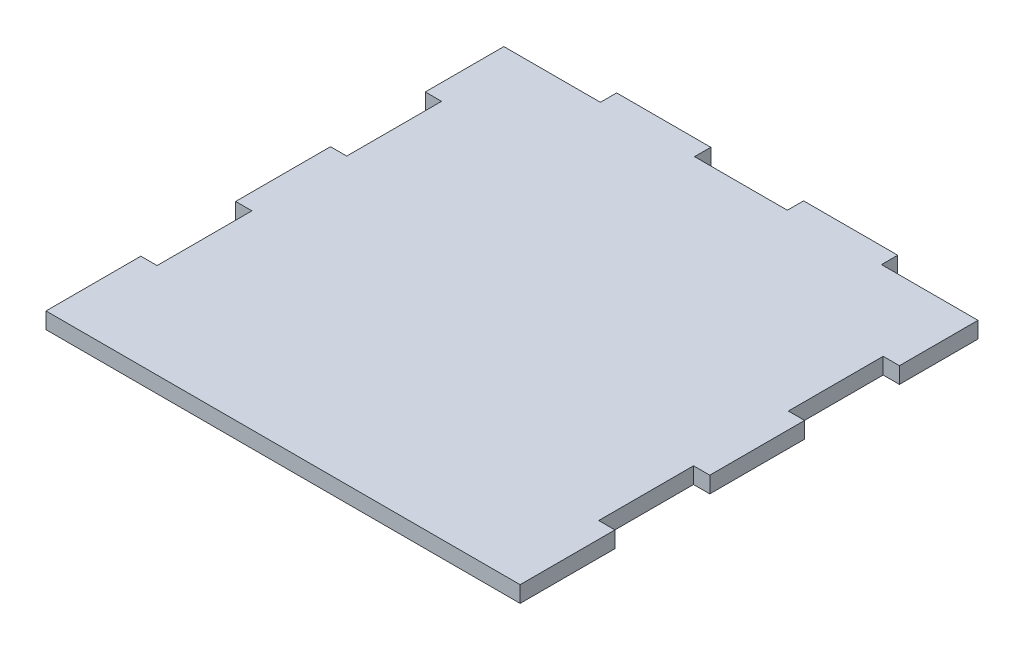
SolidWorks part; units mm, degrees
material "Maple"
ref_plane "Front Plane" through (0, 0, 0) normal (0, 0, 1) x (1, 0, 0)
ref_plane "Top Plane" through (0, 0, 0) normal (0, 1, 0) x (1, 0, 0)
ref_plane "Right Plane" through (0, 0, 0) normal (1, 0, 0) x (0, 0, -1)
sketch "Sketch1" plane through (0, 0, 0) normal (0, 1, 0) x (1, 0, 0)
  line L0 (209.25, 350) -> (278.75, 350)
  line L1 (0, 0) -> (350, 0)
  line L2 (0, 0) -> (0, 70)
  line L3 (71.25, 350) -> (140.75, 350)
  line L4 (350, 0) -> (350, 70)
  line L7 (0, 338) -> (71.25, 338)
  line L8 (71.25, 350) -> (71.25, 338)
  line L11 (350, 338) -> (278.75, 338)
  line L12 (278.75, 350) -> (278.75, 338)
  line L14 (140.75, 350) -> (140.75, 338)
  line L15 (140.75, 338) -> (209.25, 338)
  line L16 (209.25, 350) -> (209.25, 338)
  line L17 (0, 280) -> (0, 338)
  line L18 (0, 280) -> (12, 280)
  line L20 (0, 210) -> (12, 210)
  line L21 (12, 280) -> (12, 210)
  line L22 (0, 140) -> (12, 140)
  line L24 (0, 70) -> (12, 70)
  line L25 (12, 140) -> (12, 70)
  line L26 (0, 140) -> (0, 210)
  line L28 (350, 140) -> (350, 210)
  line L29 (338, 140) -> (338, 70)
  line L30 (350, 70) -> (338, 70)
  line L31 (350, 140) -> (338, 140)
  line L32 (338, 280) -> (338, 210)
  line L33 (350, 210) -> (338, 210)
  line L34 (350, 280) -> (338, 280)
  line L35 (350, 280) -> (350, 338)
  line L36 (350, 0) -> (350, 70)
  line L37 (350, 280) -> (350, 338)
  line L38 (350, 140) -> (350, 210)
  point P15 (71.25, 344)
  dimension "D1" = 350
  dimension "D2" = 338
  dimension "D3" = 71.25
  dimension "D4" = 69.5
  dimension "D5" = 71.25
  dimension "D6" = 12
  dimension "D7" = 69.5
  dimension "D8" = 70
  dimension "D9" = 70
  dimension "D10" = 70
  dimension "D11" = 70
  dimension "D12" = 12
  dimension "D13" = 12
  dimension "D14" = 70
  dimension "D15" = 70
  dimension "D16" = 70
  dimension "D17" = 70
extrude "Boss-Extrude1" add sketch "Sketch1" along normal blind 12 contours L34 L35 L11 L12 L0 L16 L15 L14 L3 L8 L7 L17 L18 L21 L20 L26 L22 L25 L24 L2 L1 L4 L30 L29 L31 L28 L33 L32
